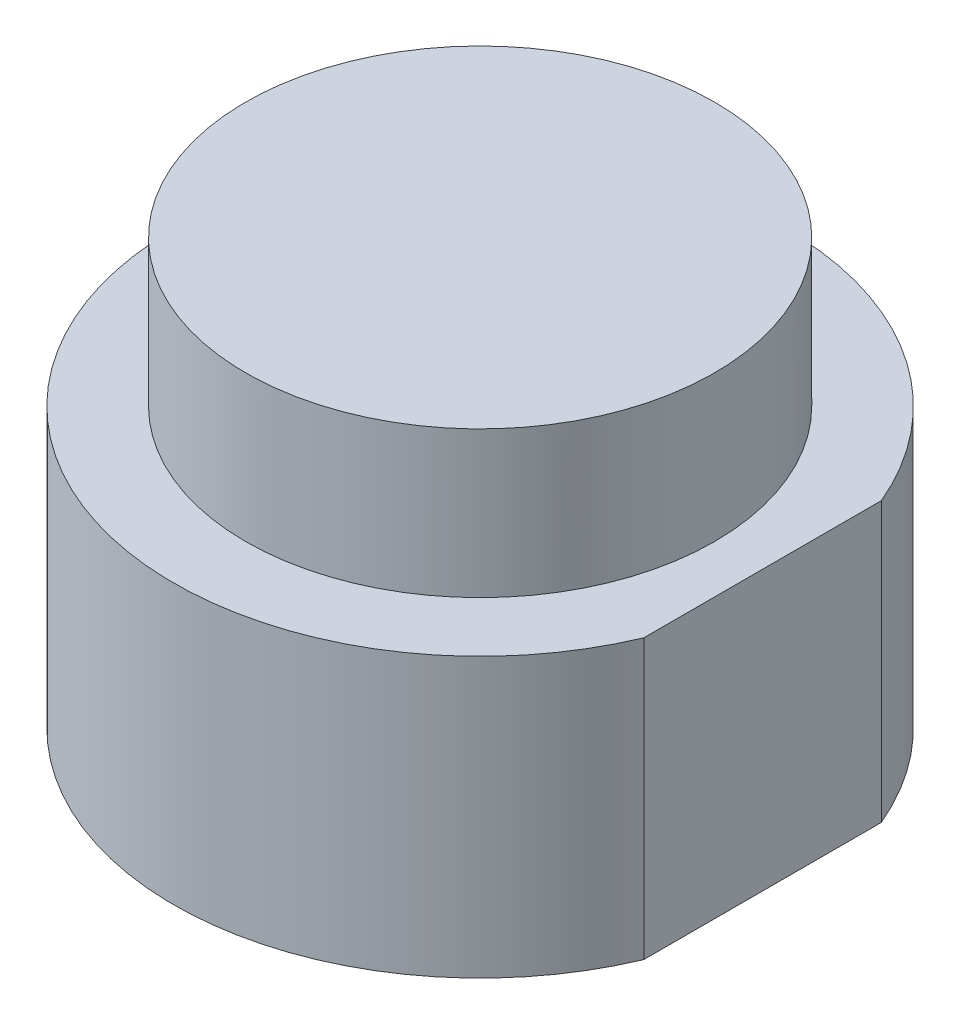
SolidWorks part; units mm, degrees
material "ABS"
ref_plane "前视基准面" through (0, 0, 0) normal (0, 0, 1) x (1, 0, 0)
ref_plane "上视基准面" through (0, 0, 0) normal (0, 1, 0) x (1, 0, 0)
ref_plane "右视基准面" through (0, 0, 0) normal (1, 0, 0) x (0, 0, -1)
other "Configuration Table"
sketch "草图1" plane through (0, 0, 0) normal (0, 1, 0) x (1, 0, 0)
  circle A0 centre (0, 0) radius 26
  dimension "D1" = 52
extrude "凸台-拉伸1" add sketch "草图1" along normal blind 23.65
sketch "草图2" plane through (0, 0, 0) normal (0, -1, 0) x (1, 0, 0)
  circle A0 centre (0, 0) radius 19.9
  dimension "D1" = 39.8
extrude "凸台-拉伸2" add sketch "草图2" against normal blind 36.05
sketch "草图3" plane through (0, 0, 0) normal (0, -1, 0) x (1, 0, 0)
  line L0 (23.9669, 10.079) -> (23.9669, -10.079)
  arc A0 (23.9669, -10.079) -> (23.9669, 10.079) centre (0, 0) ccw
  point P4 (0, 0)
  dimension "D1" = 52
extrude "切除-拉伸1" cut sketch "草图3" against normal blind 36.05
sketch "草图4" plane through (0, 0, 0) normal (0, -1, 0) x (1, 0, 0)
  line L0 (0, 0) -> (0, 19.8) construction
  line L1 (14.0007, 14.0007) -> (-14.0007, -14.0007) construction
  circle A0 centre (0, 0) radius 19.8 construction
  circle A2 centre (-14.0007, -14.0007) radius 1.25
  circle A3 centre (14.0007, 14.0007) radius 1.25
  point P7 (0, 0)
  dimension "D1" = 39.6
  dimension "D3" = 2.5
  dimension "D4" = 2.5
  dimension "D2" = 135
extrude "切除-拉伸2" cut sketch "草图4" against normal blind 2
